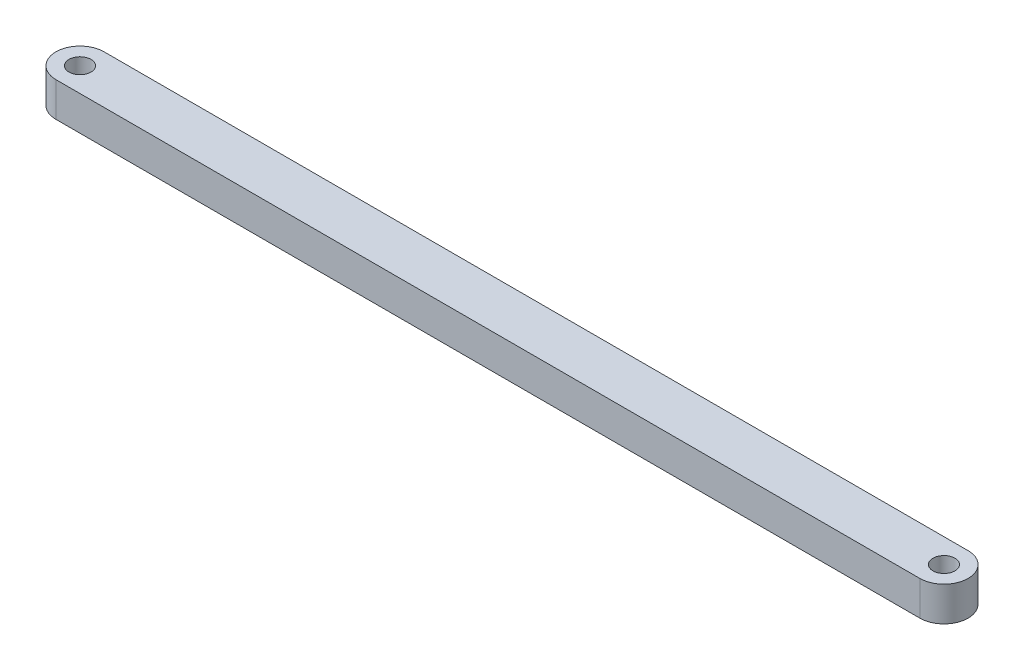
SolidWorks part; units mm, degrees
ref_plane "Front Plane" through (0, 0, 0) normal (0, 0, 1) x (1, 0, 0)
ref_plane "Top Plane" through (0, 0, 0) normal (0, 1, 0) x (1, 0, 0)
ref_plane "Right Plane" through (0, 0, 0) normal (1, 0, 0) x (0, 0, -1)
sketch "Sketch1" plane through (0, 0, 0) normal (0, 1, 0) x (1, 0, 0)
  line L0 (0, 0) -> (125.5, 0) construction
  line L1 (0, 3.5) -> (125.5, 3.5)
  line L2 (0, -3.5) -> (125.5, -3.5)
  arc A0 (0, 3.5) -> (0, -3.5) centre (0, 0) ccw
  arc A1 (125.5, -3.5) -> (125.5, 3.5) centre (125.5, 0) ccw
  circle A2 centre (0, 0) radius 1.6
  circle A3 centre (125.5, 0) radius 1.6
  point P3 (62.75, 0)
  dimension "D1" = 3.2
  dimension "D2" = 125.5
  dimension "D3" = 3.5
extrude "Boss-Extrude1" add sketch "Sketch1" along normal blind 5
